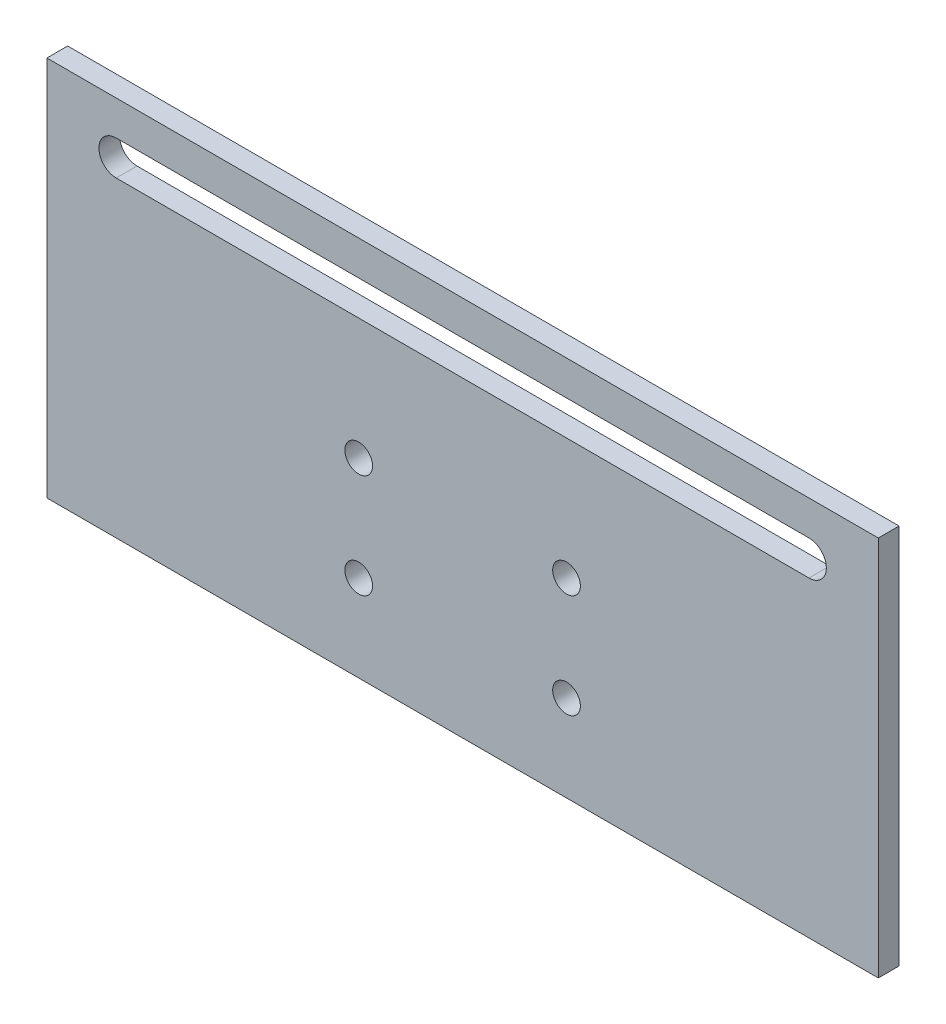
SolidWorks part; units mm, degrees
ref_plane "Front" through (0, 0, 0) normal (0, 0, 1) x (1, 0, 0)
ref_plane "Top" through (0, 0, 0) normal (0, 1, 0) x (1, 0, 0)
ref_plane "Right" through (0, 0, 0) normal (1, 0, 0) x (0, 0, -1)
sketch "Sketch1" plane through (0, 0, 0) normal (0, 0, 1) x (1, 0, 0)
  line L0 (-50, 20) -> (50, 20) construction
  line L1 (-60, 27.5) -> (60, 27.5)
  line L2 (-60, 27.5) -> (-60, -27.5)
  line L3 (-60, -27.5) -> (60, -27.5)
  line L4 (60, 27.5) -> (60, -27.5)
  line L5 (-60, 27.5) -> (60, -27.5) construction
  line L6 (-60, -27.5) -> (60, 27.5) construction
  line L7 (-50, 22.5) -> (50, 22.5)
  line L8 (-50, 17.5) -> (50, 17.5)
  line L10 (-15, 0) -> (15, 0) construction
  line L11 (-15, 0) -> (-15, -15) construction
  line L12 (-15, -15) -> (15, -15) construction
  line L13 (15, 0) -> (15, -15) construction
  arc A0 (-50, 22.5) -> (-50, 17.5) centre (-50, 20) ccw
  arc A1 (50, 17.5) -> (50, 22.5) centre (50, 20) ccw
  circle A2 centre (-15, 0) radius 2
  circle A3 centre (15, 0) radius 2
  circle A4 centre (15, -15) radius 2
  circle A5 centre (-15, -15) radius 2
  point P0 (0, 0)
  point P8 (0, 20)
  point P22 (0, 0)
  dimension "D4" = 2.5
  dimension "D8" = 4
  dimension "D1" = 120
  dimension "D2" = 55
  dimension "D3" = 100
  dimension "D5" = 20
  dimension "D6" = 15
  dimension "D7" = 30
extrude "Boss-Extrude1" add sketch "Sketch1" along normal mid plane 3
equation "\"D2@Sketch1\"=\"D5@Sketch1\"+\"D6@Sketch1\"+20"
